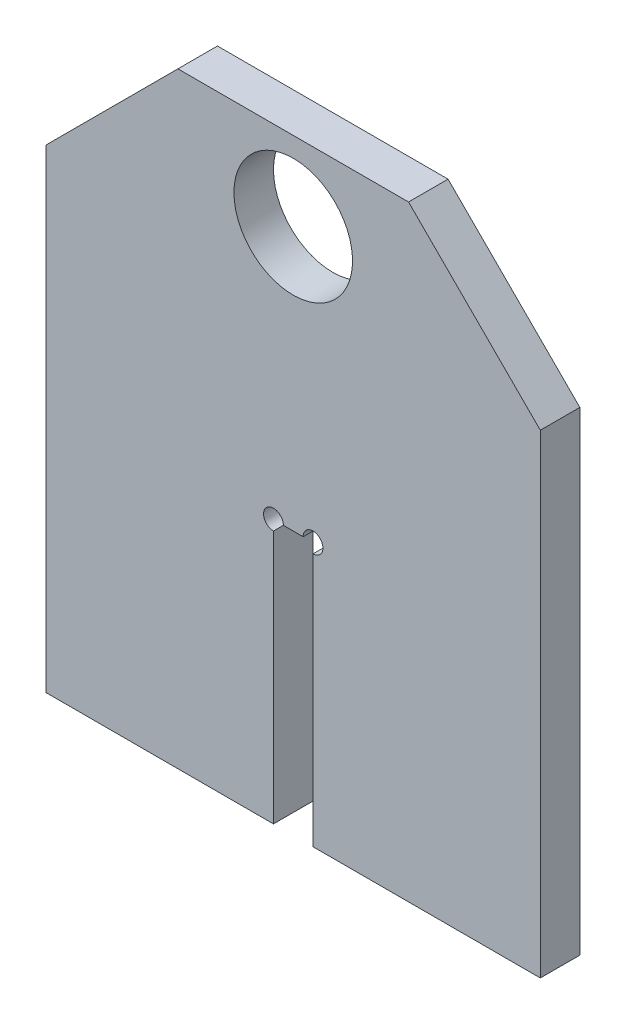
SolidWorks part; units mm, degrees
material "Plain Carbon Steel"
ref_plane "Front Plane" through (0, 0, 0) normal (0, 0, 1) x (1, 0, 0)
ref_plane "Top Plane" through (0, 0, 0) normal (0, 1, 0) x (1, 0, 0)
ref_plane "Right Plane" through (0, 0, 0) normal (1, 0, 0) x (0, 0, -1)
sketch "Sketch1" plane through (0, 0, 0) normal (0, 0, 1) x (1, 0, 0)
  line L0 (0, 221.167) -> (0, 201.5) construction
  line L1 (-3, 221.167) -> (3, 221.167) construction
  line L2 (-3, 201.5) -> (3, 201.5) construction
  line L4 (37.5, 160) -> (-37.5, 160) construction
  line L5 (37.5, 160) -> (37.5, 232)
  line L6 (17.5, 252) -> (-17.5, 252)
  line L7 (-37.5, 160) -> (-37.5, 232)
  line L8 (37.5, 160) -> (-37.5, 252) construction
  line L9 (37.5, 252) -> (-37.5, 160) construction
  line L10 (30, 220) -> (3, 220) construction
  line L11 (-13.5, 257) -> (13.5, 257) construction
  line L12 (-17.5, 252) -> (-37.5, 232)
  line L13 (37.5, 232) -> (17.5, 252)
  line L14 (-37.5, 160) -> (-3, 160)
  line L17 (-3, 160) -> (-3, 200)
  line L18 (-3, 200) -> (3, 200)
  line L19 (3, 200) -> (3, 160)
  line L20 (3, 220) -> (3, 100) construction
  line L21 (3, 160) -> (37.5, 160)
  circle A1 centre (-3, 200) radius 1.5
  circle A2 centre (3, 200) radius 1.5
  circle A4 centre (0.0001, 239.9999) radius 9
  point P6 (0, 206)
  dimension "D3" = 3
  dimension "D4" = 3
  dimension "D8" = 18
  dimension "D1" = 60
  dimension "D2" = 5
  dimension "D7" = 75
extrude "Boss-Extrude1" add sketch "Sketch1" along normal up to surface (6 mm away) contours A2 L19 L21 L5 L13 L6 L12 L7 L14 L17 A1 L18 A4
